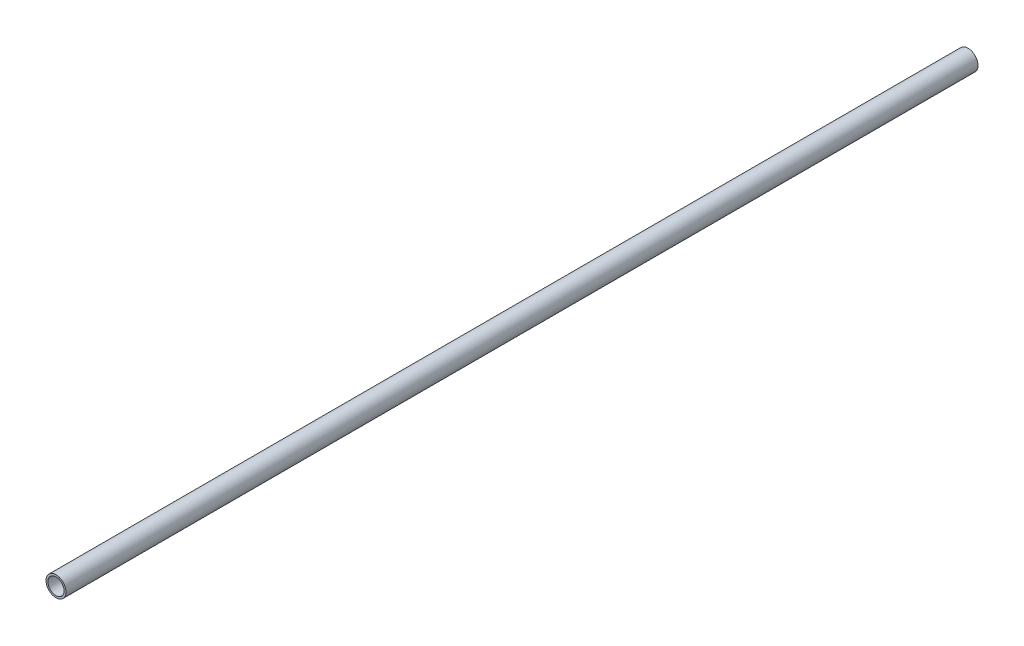
SolidWorks part; units mm, degrees
material "AISI 1020"
ref_plane "Спереди" through (0, 0, 0) normal (0, 0, 1) x (1, 0, 0)
ref_plane "Сверху" through (0, 0, 0) normal (0, 1, 0) x (1, 0, 0)
ref_plane "Справа" through (0, 0, 0) normal (1, 0, 0) x (0, 0, -1)
sketch "Эскиз1" plane through (0, 0, 0) normal (0, 0, 1) x (1, 0, 0)
  line L0 (-35, 0) -> (250, 0) construction
  arc A0 (159.8047, -104.1915) -> (208.7492, -10.65) centre (0, 39) ccw construction
  circle B0 centre (208.7492, -10.65) radius 8.65
  circle B1 centre (208.7492, -10.65) radius 10.65
  line B2 (208.7492, -10.65) -> (208.7492, -2) construction
sketch_block_instance "Труба 21_3х2-1"
sketch_block "Труба 21_3х2" parameters "D2"=21.3, "D1"=2
extrude "Бобышка-Вытянуть1" add sketch "Эскиз1" against normal up to surface (485.6 mm away) from offset 4 offset against normal yes
mirror "Зеркальное отражение1" about plane through (-190.5639, 31.462, -489.6) normal (0, 0, 1) of "Бобышка-Вытянуть1"
